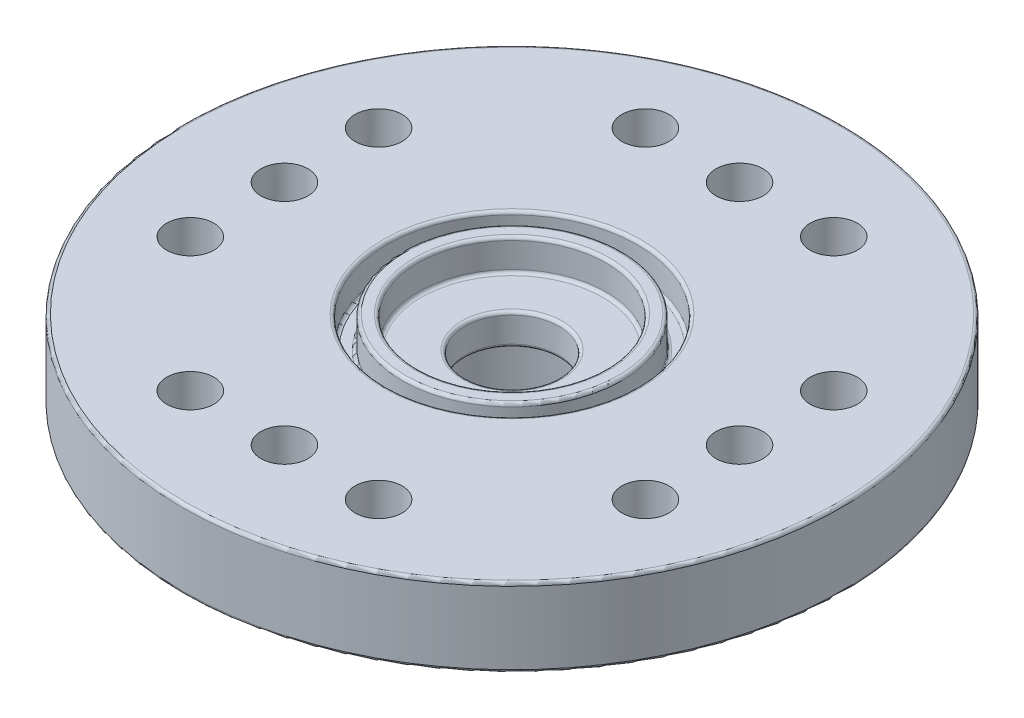
SolidWorks part; units mm, degrees
ref_plane "前视基准面" through (0, 0, 0) normal (0, 0, 1) x (1, 0, 0)
ref_plane "上视基准面" through (0, 0, 0) normal (0, 1, 0) x (1, 0, 0)
ref_plane "右视基准面" through (0, 0, 0) normal (1, 0, 0) x (0, 0, -1)
sketch "草图1" plane through (0, 0, 0) normal (0, 1, 0) x (1, 0, 0)
  circle A0 centre (0, 0) radius 10.5
  dimension "D1" = 21
extrude "凸台-拉伸1" add sketch "草图1" along normal blind 2.5
sketch "草图2" plane through (0, 2.5, 0) normal (0, 1, 0) x (1, 0, 0)
  circle A0 centre (0, 0) radius 3
  dimension "D1" = 6
extrude "切除-拉伸1" cut sketch "草图2" against normal blind 12
sketch "草图3" plane through (0, 0, 0) normal (0, -1, 0) x (1, 0, 0)
  circle A0 centre (0, 0) radius 3
  circle A1 centre (0, 0) radius 4
  dimension "D1" = 8
extrude "凸台-拉伸2" add sketch "草图3" along normal blind 3
sketch "草图4" plane through (0, 2.5, 0) normal (0, 1, 0) x (1, 0, 0)
  line L0 (0, -1.375) -> (0, 1.375) construction
  line L1 (-1.375, 0) -> (1.375, 0) construction
  circle A0 centre (0, 7.25) radius 0.75
  circle A1 centre (7.25, 0) radius 0.75
  circle A2 centre (3, 7.25) radius 0.75
  circle A3 centre (7.25, 3) radius 0.75
  circle A4 centre (-3, 7.25) radius 0.75
  circle A5 centre (7.25, -3) radius 0.75
  circle A6 centre (3, -7.25) radius 0.75
  circle A7 centre (0, -7.25) radius 0.75
  circle A8 centre (-3, -7.25) radius 0.75
  circle A9 centre (-7.25, -3) radius 0.75
  circle A10 centre (-7.25, 0) radius 0.75
  circle A11 centre (-7.25, 3) radius 0.75
  dimension "D3" = 1.5
  dimension "D4" = 1.5
  dimension "D1" = 7.25
  dimension "D2" = 7.25
  dimension "D5" = 3
  dimension "D6" = 3
extrude "切除-拉伸2" cut sketch "草图4" against normal blind 3
sketch "草图5" plane through (0, 2.5, 0) normal (0, 1, 0) x (1, 0, 0)
  circle A0 centre (0, 0) radius 3
extrude "凸台-拉伸3" add sketch "草图5" against normal blind 2
sketch "草图6" plane through (0, 2.5, 0) normal (0, 1, 0) x (1, 0, 0)
  circle A0 centre (0, 0) radius 3
  dimension "D1" = 6
extrude "切除-拉伸3" cut sketch "草图6" against normal blind 1
sketch "草图7" plane through (0, 1.5, 0) normal (0, 1, 0) x (1, 0, 0)
  circle A0 centre (0, 0) radius 1.5
  dimension "D1" = 3
extrude "切除-拉伸5" cut sketch "草图7" against normal blind 1
sketch "草图8" plane through (0, 2.5, 0) normal (0, 1, 0) x (1, 0, 0)
  circle A0 centre (0, 0) radius 4
  circle A1 centre (0, 0) radius 3.5
  dimension "D1" = 8
  dimension "D2" = 7
extrude "切除-拉伸6" cut sketch "草图8" against normal blind 1
fillet "圆角1" radius 0.1 12 edges at (0, -3, -3) (0, -3, -4) (0, 0.5, 1.5) (0, 1.5, 1.5) (0, 1.5, 3) (0, 1.5, 3.5) (0, 1.5, 4) (0, 2.5, 3) (0, 2.5, 3.5) (0, 2.5, 4) (0, 0, 10.5) (0, 2.5, 10.5)
